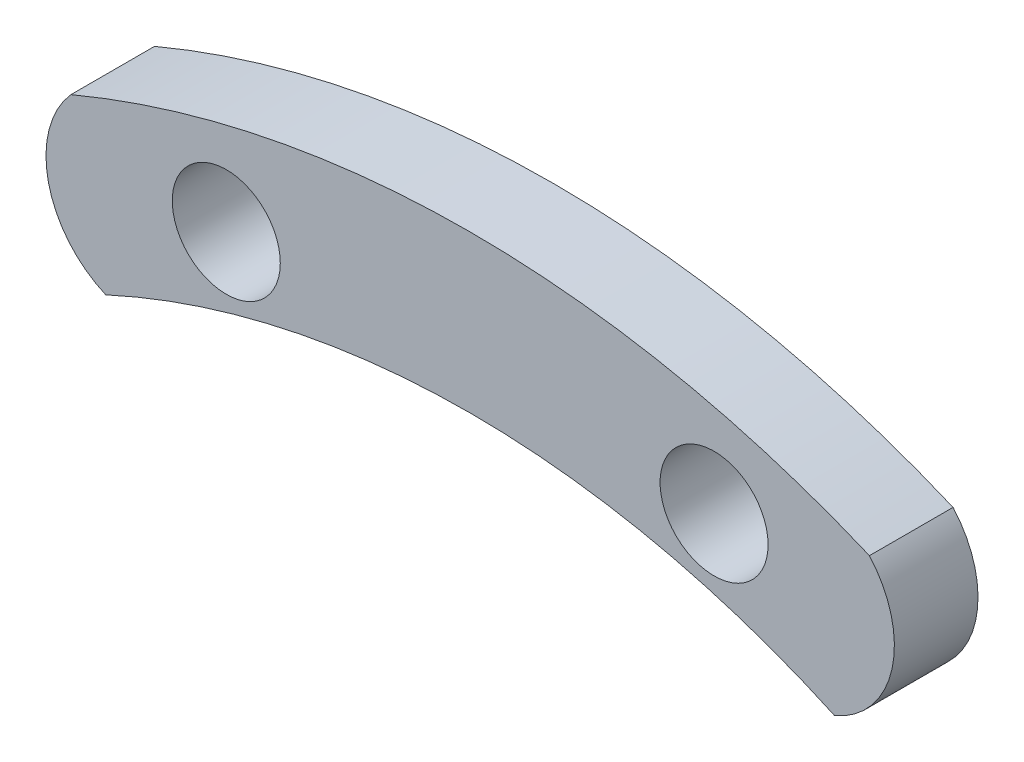
SolidWorks part; units mm, degrees
ref_plane "Front Plane" through (0, 0, 0) normal (0, 0, 1) x (1, 0, 0)
ref_plane "Top Plane" through (0, 0, 0) normal (0, 1, 0) x (1, 0, 0)
ref_plane "Right Plane" through (0, 0, 0) normal (1, 0, 0) x (0, 0, -1)
sketch "Sketch1" plane through (0, 0, 0) normal (0, 0, 1) x (1, 0, 0)
  line L1 (0, 96.3712) -> (0, -9.4867) construction
  line L2 (-17.78, 62.3738) -> (-14.605, 64.2069)
  line L3 (-14.605, 64.2069) -> (-14.605, 67.8731)
  line L4 (-14.605, 67.8731) -> (-17.78, 69.7062)
  line L5 (-17.78, 69.7062) -> (-20.955, 67.8731)
  line L6 (-20.955, 67.8731) -> (-20.955, 64.2069)
  line L7 (-20.955, 64.2069) -> (-17.78, 62.3738)
  line L8 (17.78, 62.3738) -> (20.955, 64.2069)
  line L9 (20.955, 64.2069) -> (20.955, 67.8731)
  line L10 (20.955, 67.8731) -> (17.78, 69.7062)
  line L11 (17.78, 69.7062) -> (14.605, 67.8731)
  line L12 (14.605, 67.8731) -> (14.605, 64.2069)
  line L13 (14.605, 64.2069) -> (17.78, 62.3738)
  arc A0 (29.1049, 69.0464) -> (-29.1049, 69.0464) centre (0, 0) ccw
  circle A1 centre (-17.78, 66.04) radius 1.5 construction
  circle A2 centre (17.78, 66.04) radius 1.5 construction
  arc A3 (26.5655, 57.676) -> (-26.5655, 57.676) centre (0, 0) ccw
  arc A4 (-29.1049, 69.0464) -> (-26.5655, 57.676) centre (-23.7487, 64.2739) ccw
  circle A5 centre (-17.78, 66.04) radius 3.175 construction
  arc A6 (29.1049, 69.0464) -> (26.5655, 57.676) centre (23.7487, 64.2739) cw
  circle A7 centre (17.78, 66.04) radius 3.175 construction
  dimension "D1" = 149.86
  dimension "D2" = 6.35
  dimension "D3" = 17.78
  dimension "D4" = 3
  dimension "D6" = 127
  dimension "D7" = 6.35
  dimension "D5" = 66.04
sketch "Sketch2" plane through (0, 0, 0) normal (0, 0, 1) x (1, 0, 0)
  line L1 (0, 96.3712) -> (0, -9.4867) construction
  arc A0 (29.1049, 69.0464) -> (-29.1049, 69.0464) centre (0, 0) ccw
  circle A1 centre (-17.78, 66.04) radius 1.5 construction
  circle A2 centre (17.78, 66.04) radius 1.5 construction
  arc A3 (26.5655, 57.676) -> (-26.5655, 57.676) centre (0, 0) ccw
  arc A4 (-29.1049, 69.0464) -> (-26.5655, 57.676) centre (-23.7487, 64.2739) ccw
  circle A5 centre (17.78, 66.04) radius 3.937
  arc A6 (29.1049, 69.0464) -> (26.5655, 57.676) centre (23.7487, 64.2739) cw
  circle A8 centre (-17.78, 66.04) radius 3.937
  dimension "D1" = 149.86
  dimension "D2" = 7.874
  dimension "D3" = 17.78
  dimension "D4" = 3
  dimension "D6" = 127
  dimension "7mm" = 7.874
  dimension "D5" = 66.04
extrude "Boss-Extrude4" add sketch "Sketch2" along normal blind 6.096
